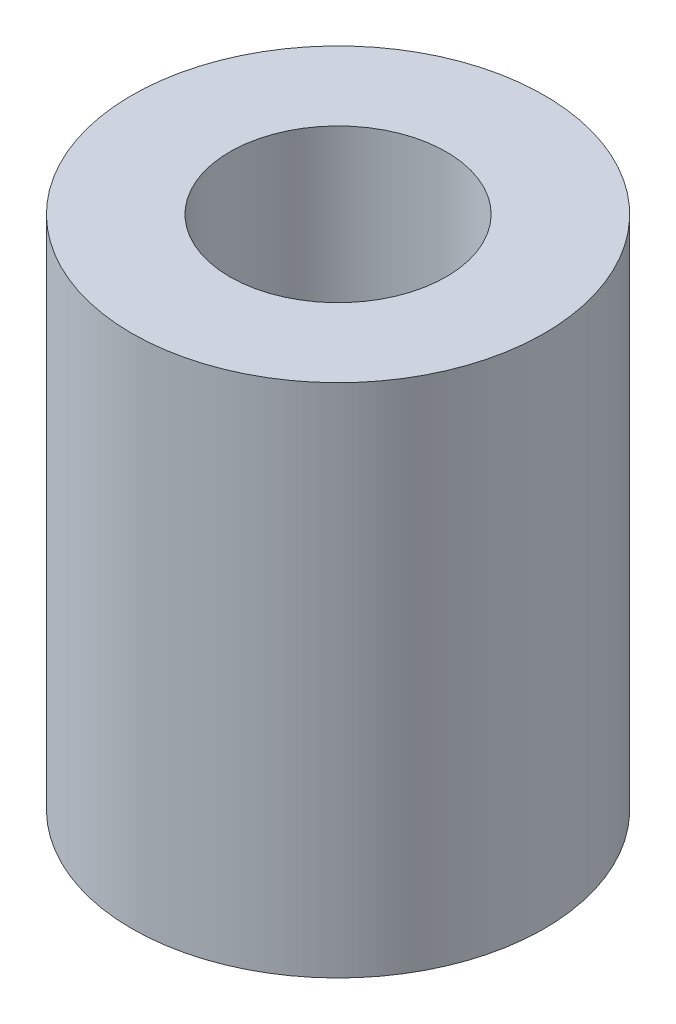
SolidWorks part; units mm, degrees
ref_plane "Front Plane" through (0, 0, 0) normal (0, 0, 1) x (1, 0, 0)
ref_plane "Top Plane" through (0, 0, 0) normal (0, 1, 0) x (1, 0, 0)
ref_plane "Right Plane" through (0, 0, 0) normal (1, 0, 0) x (0, 0, -1)
sketch "Sketch1" plane through (0, 0, 0) normal (0, 1, 0) x (1, 0, 0)
  circle A0 centre (0, 0) radius 4
  circle A1 centre (0, 0) radius 2.1
  dimension "D1" = 8
  dimension "D2" = 4.2
extrude "Boss-Extrude1" add sketch "Sketch1" along normal blind 10
